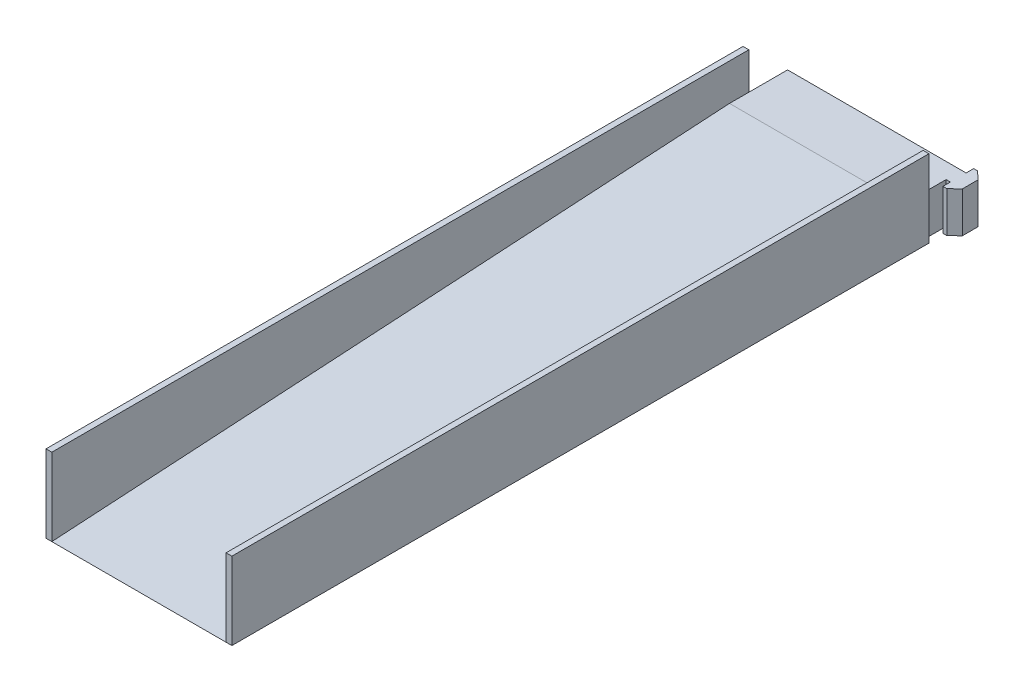
SolidWorks part; units mm, degrees
ref_plane "Front Plane" through (0, 0, 0) normal (0, 0, 1) x (1, 0, 0)
ref_plane "Top Plane" through (0, 0, 0) normal (0, 1, 0) x (1, 0, 0)
ref_plane "Right Plane" through (0, 0, 0) normal (1, 0, 0) x (0, 0, -1)
sketch "Sketch1" plane through (0, 0, 0) normal (0, 1, 0) x (1, 0, 0)
  line L0 (47.2, 190) -> (45, 190)
  line L1 (-45, -190) -> (45, -190)
  line L2 (-45, -190) -> (-45, 190)
  line L3 (-45, 190) -> (45, 190)
  line L4 (45, -190) -> (45, 190)
  line L5 (-45, -190) -> (45, 190) construction
  line L6 (-45, 190) -> (45, -190) construction
  line L7 (47.2, 181.9) -> (45, 181.9)
  point P0 (0, 0)
  line B0 (47.2, 193.9) -> (49.24, 193.9)
  line B1 (53.3524, 189.998) -> (53.3524, 181.902)
  line B2 (49.24, 178) -> (47.2, 178)
  line B3 (47.2, 178) -> (47.2, 193.9)
  line B4 (49.24, 193.9) -> (53.3524, 189.998)
  line B5 (53.3524, 181.902) -> (49.24, 178)
  line B6 (47.2, 190) -> (47.2, 181.9) construction
  dimension "D1" = 90
  dimension "D2" = 380
  dimension "D3" = 2.2
sketch_block_instance "Extrusion Profile-2"
sketch_block "Extrusion Profile" parameters "D1"=8.44, "D2"=2.6, "D3"=6, "D4"=16.7, "D6"=5.6686, "D7"=2.0404, "D8"=8.0963, "D9"=15.9, "D5"=2.4157
extrude "Boss-Extrude1" add sketch "Sketch1" along normal blind 21 contours L1 L4 L3 L2 | L7 B3 L0 L4 | B2 B5 B1 B4 B0 B3
sketch "Sketch3" plane through (-45, 0, 0) normal (-1, 0, 0) x (0, 0, 1)
  line L0 (190, 0) -> (-160, 21)
  line L1 (190, 21) -> (-190, 21) construction
  line L2 (-160, 21) -> (190, 21)
  line L3 (190, 21) -> (190, 0)
  dimension "D1" = 30
extrude "Cut-Extrude1" cut sketch "Sketch3" against normal through all
sketch "Sketch2" plane through (0, 0, 0) normal (0, -1, 0) x (1, 0, 0)
  line L0 (-45, 190) -> (-45, -190) construction
  line L1 (-45, -170) -> (-48, -170)
  line L2 (-45, -170) -> (-45, 190)
  line L3 (-45, 190) -> (-48, 190)
  line L4 (-48, -170) -> (-48, 190)
  line L5 (-45, -190) -> (47.2, -190) construction
  line L6 (-45, 190) -> (45, 190) construction
  point P8 (0, 0)
  dimension "D1" = 20
  dimension "D2" = 3
extrude "Boss-Extrude2" add sketch "Sketch2" against normal blind 40
mirror "Mirror1" about plane through (0, 0, 0) normal (1, 0, 0) of "Boss-Extrude2"
